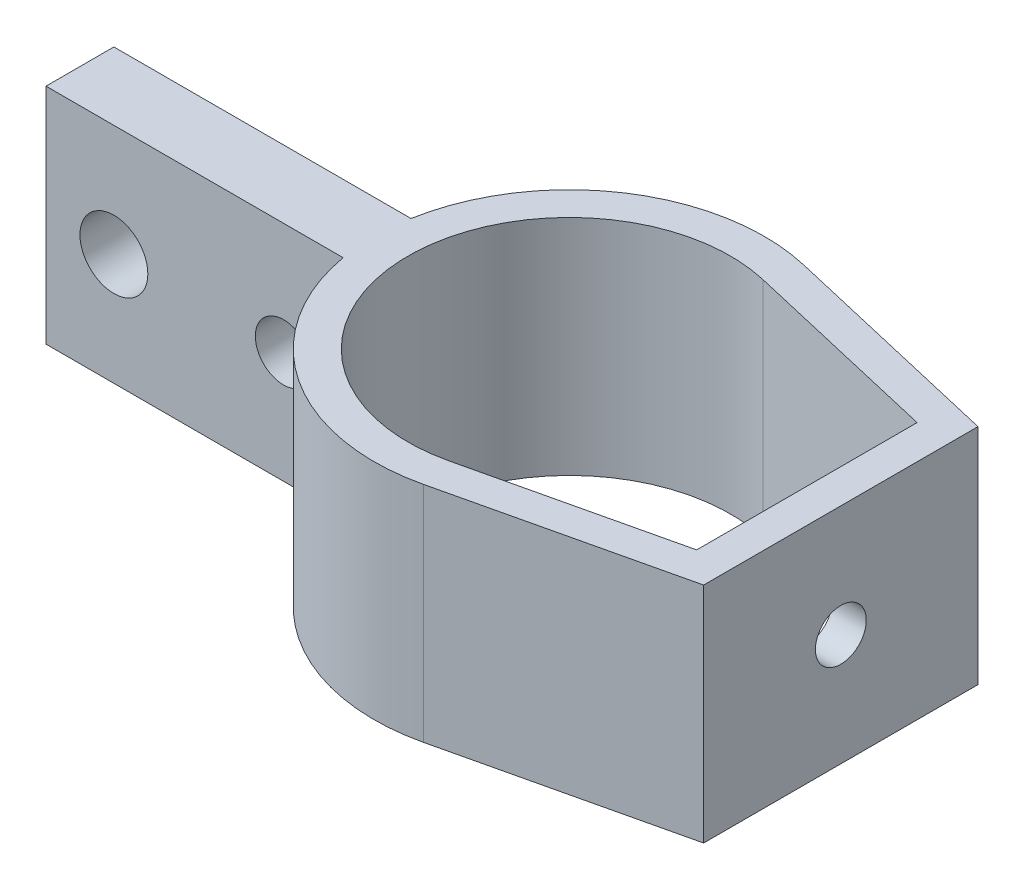
SolidWorks part; units mm, degrees
ref_plane "前视基准面" through (0, 0, 0) normal (0, 0, 1) x (1, 0, 0)
ref_plane "上视基准面" through (0, 0, 0) normal (0, 1, 0) x (1, 0, 0)
ref_plane "右视基准面" through (0, 0, 0) normal (1, 0, 0) x (0, 0, -1)
other "Configuration Table"
sketch "Sketch1" plane through (0, 0, 0) normal (0, 1, 0) x (1, 0, 0)
  line L0 (0, 0) -> (-17.526, 0) construction
  line L1 (0, 0) -> (24.384, 0) construction
  line L2 (24.384, -12.319) -> (24.384, 12.319)
  line L3 (24.384, 12.319) -> (3.973, 17.0697)
  line L4 (24.384, -12.319) -> (3.973, -17.0697)
  line L5 (-17.526, 0) -> (-43.942, 0) construction
  line L6 (-43.942, -3.048) -> (-43.942, 3.048)
  line L7 (-43.942, 3.048) -> (-17.2589, 3.048)
  line L8 (-43.942, -3.048) -> (-17.2589, -3.048)
  line L9 (24.384, 0) -> (21.336, 0) construction
  line L10 (21.336, -9.899) -> (21.336, 9.899)
  line L11 (0, 0) -> (3.973, 17.0697) construction
  line L12 (3.2821, 14.1011) -> (21.336, 9.899)
  line L13 (3.2821, -14.1011) -> (21.336, -9.899)
  arc A0 (3.973, 17.0697) -> (-17.2589, 3.048) centre (0, 0) ccw
  arc A1 (3.2821, 14.1011) -> (3.2821, -14.1011) centre (0, 0) ccw
  arc A2 (-17.2589, -3.048) -> (3.973, -17.0697) centre (0, 0) ccw
  dimension "D1" = 35.052
  dimension "D4" = 28.956
  dimension "D2" = 24.384
  dimension "D3" = 12.319
  dimension "D5" = 26.416
  dimension "D6" = 3.048
  dimension "D7" = 3.048
extrude "Boss-Extrude1" add sketch "Sketch1" along normal mid plane 20.066
sketch "Sketch2" plane through (0, 0, 3.048) normal (0, 0, 1) x (1, 0, 0)
  line L0 (-43.942, 0) -> (-37.846, 0) construction
  line L1 (-43.942, 10.033) -> (-43.942, -10.033) construction
  line L2 (-37.846, 0) -> (-22.606, 0) construction
  circle A0 centre (-37.846, 0) radius 3.048
  circle A1 centre (-22.606, 0) radius 2.54
  dimension "D3" = 6.096
  dimension "D4" = 5.08
  dimension "D1" = 6.096
  dimension "D2" = 15.24
extrude "Cut-Extrude1" cut sketch "Sketch2" against normal mid plane 20.066
sketch "Sketch3" plane through (24.384, 0, 0) normal (1, 0, 0) x (0, 0, -1)
  circle A0 centre (0, 0) radius 2.286
  dimension "D1" = 4.572
extrude "Cut-Extrude2" cut sketch "Sketch3" against normal mid plane 20.066
